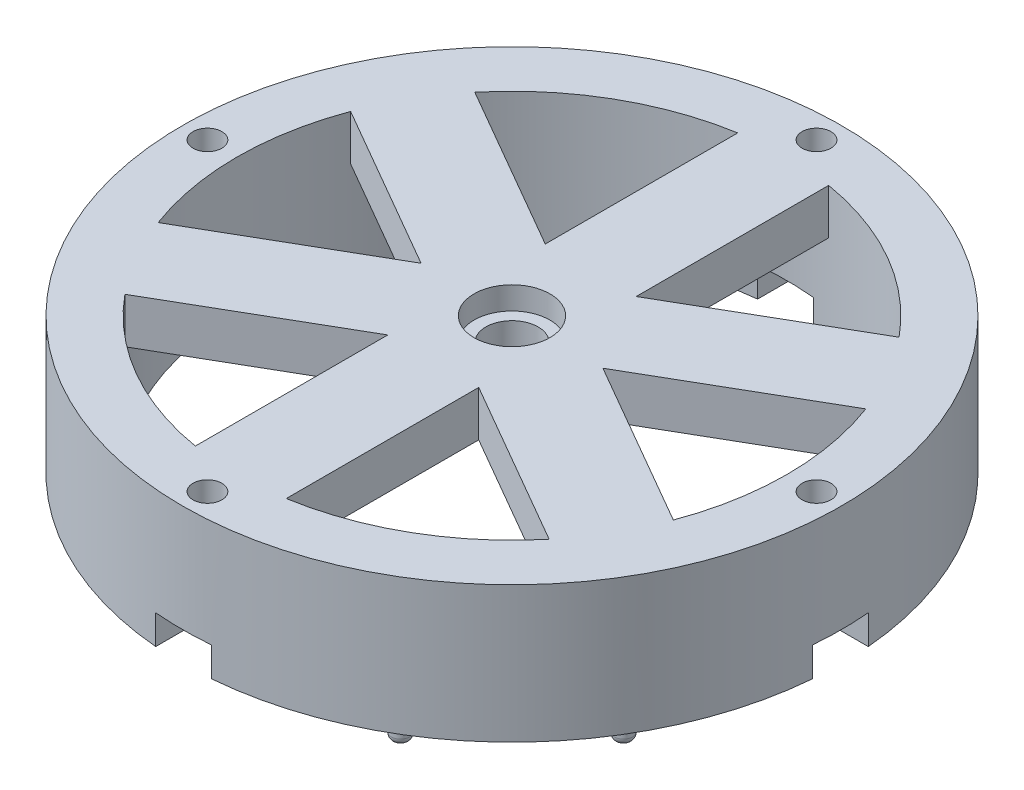
SolidWorks part; units mm, degrees
ref_plane "Front Plane" through (0, 0, 0) normal (0, 0, 1) x (1, 0, 0)
ref_plane "Top Plane" through (0, 0, 0) normal (0, 1, 0) x (1, 0, 0)
ref_plane "Right Plane" through (0, 0, 0) normal (1, 0, 0) x (0, 0, -1)
sketch "Sketch1" plane through (0, 0, 0) normal (0, 1, 0) x (1, 0, 0)
  line L24 (10, 17.3205) -> (10, 59.6678)
  line L34 (10, 17.3205) -> (46.6739, 38.4942)
  line L36 (-10, 17.3205) -> (-10, 59.6678)
  line L37 (-10, 17.3205) -> (-46.6739, 38.4942)
  line L38 (-20, 0) -> (-56.6739, 21.1737)
  line L39 (-20, 0) -> (-56.6739, -21.1737)
  line L40 (-10, -17.3205) -> (-46.6739, -38.4942)
  line L41 (-10, -17.3205) -> (-10, -59.6678)
  line L42 (10, -17.3205) -> (10, -59.6678)
  line L43 (10, -17.3205) -> (46.6739, -38.4942)
  line L44 (20, 0) -> (56.6739, 21.1737)
  line L45 (20, 0) -> (56.6739, -21.1737)
  circle A3 centre (0, 67) radius 3.175
  circle A13 centre (67, 0) radius 3.175
  circle A14 centre (0, -67) radius 3.175
  circle A15 centre (-67, 0) radius 3.175
  arc A16 (46.6739, 38.4942) -> (10, 59.6678) centre (0, 0) ccw
  arc A17 (-10, 59.6678) -> (-46.6739, 38.4942) centre (0, 0) ccw
  arc A18 (-56.6739, 21.1737) -> (-56.6739, -21.1737) centre (0, 0) ccw
  arc A19 (-46.6739, -38.4942) -> (-10, -59.6678) centre (0, 0) ccw
  arc A20 (10, -59.6678) -> (46.6739, -38.4942) centre (0, 0) ccw
  arc A21 (56.6739, -21.1737) -> (56.6739, 21.1737) centre (0, 0) ccw
  circle A23 centre (0, 0) radius 72.5
  point P24 (0, 0)
  point P35 (0, 0)
  point P46 (0, 0)
  point P68 (0, 0)
  dimension "D1" = 145
  dimension "D2" = 4
  dimension "D6" = 6.35
extrude "Boss-Extrude1" add sketch "Sketch1" along normal blind 10
sketch "Sketch8" plane through (0, 10, 0) normal (0, 1, 0) x (1, 0, 0)
  circle A0 centre (0, 0) radius 8.35
  dimension "D1" = 16.7
extrude "Cut-Extrude4" cut sketch "Sketch8" against normal blind 5
sketch "Sketch9" plane through (0, 10, 0) normal (0, 1, 0) x (1, 0, 0)
  circle A0 centre (0, 0) radius 5.75
  dimension "D1" = 11.5
extrude "Cut-Extrude5" cut sketch "Sketch9" against normal through all both and the other way through all
sketch "Sketch10" plane through (0, 0, 0) normal (0, -1, 0) x (1, 0, 0)
  circle A0 centre (0, 0) radius 60.5
  circle A1 centre (0, 0) radius 72.5
  circle A3 centre (0, -67) radius 3.175
  circle A4 centre (-67, 0) radius 3.175
  circle A5 centre (0, 67) radius 3.175
  circle A6 centre (67, 0) radius 3.175
  point P16 (0, 0)
  dimension "D2" = 145
  dimension "D1" = 4
extrude "Boss-Extrude4" add sketch "Sketch10" along normal blind 20
sketch "Sketch11" plane through (0, -20, 0) normal (0, -1, 0) x (1, 0, 0)
  line L0 (0, 0) -> (0, -60.5)
  line L1 (-44.3636, -6.15) -> (-44.3636, 6.15)
  line L2 (6.15, -44.3636) -> (-6.15, -44.3636)
  line L3 (6.15, -44.3636) -> (6.15, -76.6364)
  line L4 (6.15, -76.6364) -> (-6.15, -76.6364)
  line L5 (-6.15, -44.3636) -> (-6.15, -76.6364)
  line L6 (6.15, -44.3636) -> (-6.15, -76.6364) construction
  line L7 (6.15, -76.6364) -> (-6.15, -44.3636) construction
  line L8 (-44.3636, -6.15) -> (-76.6364, -6.15)
  line L9 (-76.6364, -6.15) -> (-76.6364, 6.15)
  line L10 (-44.3636, 6.15) -> (-76.6364, 6.15)
  line L11 (-44.3636, -6.15) -> (-76.6364, 6.15) construction
  line L12 (-76.6364, -6.15) -> (-44.3636, 6.15) construction
  line L13 (0, 0) -> (-60.5, 0)
  line L14 (-6.15, 44.3636) -> (6.15, 44.3636)
  line L15 (-6.15, 44.3636) -> (-6.15, 76.6364)
  line L16 (-6.15, 76.6364) -> (6.15, 76.6364)
  line L17 (6.15, 44.3636) -> (6.15, 76.6364)
  line L18 (-6.15, 44.3636) -> (6.15, 76.6364) construction
  line L19 (-6.15, 76.6364) -> (6.15, 44.3636) construction
  line L20 (0, 0) -> (0, 60.5)
  line L21 (44.3636, 6.15) -> (44.3636, -6.15)
  line L22 (44.3636, 6.15) -> (76.6364, 6.15)
  line L23 (76.6364, 6.15) -> (76.6364, -6.15)
  line L24 (44.3636, -6.15) -> (76.6364, -6.15)
  line L25 (44.3636, 6.15) -> (76.6364, -6.15) construction
  line L26 (76.6364, 6.15) -> (44.3636, -6.15) construction
  line L27 (0, 0) -> (60.5, 0)
  circle A0 centre (0, 0) radius 60.5 construction
  point P28 (0, 0)
  dimension "D1" = 12.3
  dimension "D2" = 4
extrude "Cut-Extrude6" cut sketch "Sketch11" against normal blind 6.45 contours L3 L4 L5 L2 | L10 L9 L8 L1 | L17 L16 L15 L14 | L22 L23 L24 L21
sketch "Sketch12" plane through (0, -20, 0) normal (0, -1, 0) x (1, 0, 0)
  line L0 (0, 0) -> (0, 67)
  line L1 (0, 0) -> (33.5, 58.0237)
  line L2 (0, 0) -> (58.0237, 33.5)
  line L3 (0, 0) -> (67, 0)
  circle A0 centre (0, 0) radius 67
  circle A1 centre (33.5, 58.0237) radius 2
  circle A2 centre (58.0237, 33.5) radius 2
  circle A3 centre (33.5, -58.0237) radius 2
  circle A4 centre (58.0237, -33.5) radius 2
  circle A5 centre (-58.0237, -33.5) radius 2
  circle A6 centre (-33.5, -58.0237) radius 2
  circle A7 centre (-33.5, 58.0237) radius 2
  circle A8 centre (-58.0237, 33.5) radius 2
  point P25 (0, 0)
  dimension "D3" = 4
  dimension "D4" = 4
  dimension "D5" = 4
  dimension "D1" = 30
  dimension "D2" = 30
extrude "Boss-Extrude5" add sketch "Sketch12" along normal blind 5 contours A1 | A2 | A4 | A3 | A6 | A5 | A8 | A7
fillet "Fillet1" radius 1.5 8 edges at (33.5, -25, 56.0237) (-58.0237, -25, -35.5) (-33.5, -25, -60.0237) (33.5, -25, -60.0237) (58.0237, -25, -35.5) (58.0237, -25, 31.5) (-33.5, -25, 56.0237) (-58.0237, -25, 31.5)
